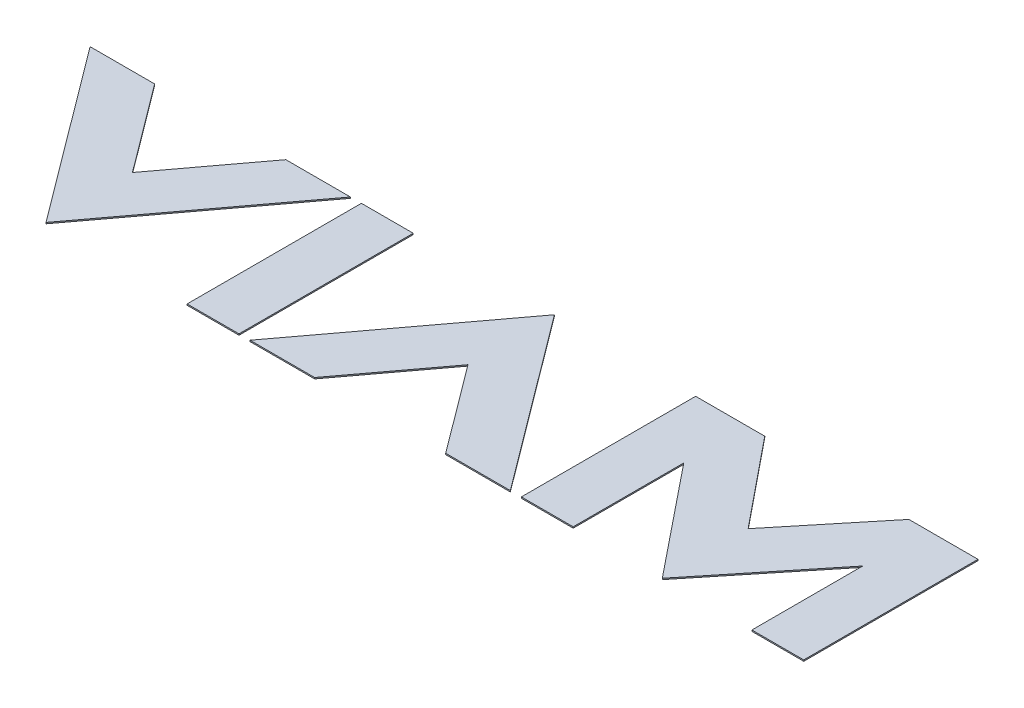
SolidWorks part; units mm, degrees
ref_plane "Front Plane" through (0, 0, 0) normal (0, 0, 1) x (1, 0, 0)
ref_plane "Top Plane" through (0, 0, 0) normal (0, 1, 0) x (1, 0, 0)
ref_plane "Right Plane" through (0, 0, 0) normal (1, 0, 0) x (0, 0, -1)
sketch "Sketch1" plane through (0, 0, 0) normal (0, 1, 0) x (1, 0, 0)
  line L0 (-15, 0) -> (15, 0) construction
  line L1 (-15, 10) -> (15, 10) construction
  line L2 (-15, -10) -> (15, -10) construction
  line L4 (37.5, -12.5) -> (-37.5, -12.5)
  line L5 (37.5, -12.5) -> (37.5, 12.5)
  line L6 (37.5, 12.5) -> (-37.5, 12.5)
  line L7 (-37.5, -12.5) -> (-37.5, 12.5)
  line L8 (37.5, -12.5) -> (-37.5, 12.5) construction
  line L9 (37.5, 12.5) -> (-37.5, -12.5) construction
  arc A0 (-15, 10) -> (-15, -10) centre (-15, 0) ccw construction
  arc A1 (15, -10) -> (15, 10) centre (15, 0) ccw construction
  point P2 (0, 0)
  point P8 (0, 0)
  dimension "D1" = 10
  dimension "D2" = 30
  dimension "D3" = 75
  dimension "D4" = 25
sketch "Sketch2" plane through (-16.7784, 0, 2.9159) normal (0, 1, 0) x (1, 0, 0)
  line L0 (2.563, 10.2) -> (6.7344, 10.2)
  line L1 (6.7344, 10.2) -> (6.7344, -3.8188)
  line L2 (6.7344, -3.8188) -> (2.563, -3.8188)
  line L3 (2.563, -3.8188) -> (2.563, 10.2)
  line L4 (46.612, 10.2) -> (40.7912, 3.0852)
  line L5 (40.7912, 3.0852) -> (35.0159, 10.2)
  line L6 (35.0159, 10.2) -> (29.4555, 10.2)
  line L7 (29.4555, 10.2) -> (29.4555, -3.8188)
  line L8 (29.4555, -3.8188) -> (33.6227, -3.8188)
  line L9 (33.6227, -3.8188) -> (33.6227, 5.0778)
  line L10 (33.6227, 5.0778) -> (40.7912, -3.8188)
  line L11 (40.7912, -3.8188) -> (48.0011, 5.0985)
  line L12 (48.0011, 5.0985) -> (48.0011, -3.8188)
  line L13 (48.0011, -3.8188) -> (52.1724, -3.8188)
  line L14 (52.1724, -3.8188) -> (52.1724, 10.2)
  line L15 (52.1724, 10.2) -> (46.612, 10.2)
  line L16 (-3.5183, 10.2) -> (-8.7934, 3.1348)
  line L17 (-8.7934, 3.1348) -> (-14.0685, 10.2)
  line L18 (-14.0685, 10.2) -> (-19.2651, 10.2)
  line L19 (-19.2651, 10.2) -> (-8.7934, -3.8188)
  line L20 (-8.7934, -3.8188) -> (1.6784, 10.2)
  line L21 (1.6784, 10.2) -> (-3.5183, 10.2)
  line L22 (18.095, 10.2) -> (7.6233, -3.8188)
  line L23 (7.6233, -3.8188) -> (12.8198, -3.8188)
  line L24 (12.8198, -3.8188) -> (18.095, 3.2423)
  line L25 (18.095, 3.2423) -> (23.3701, -3.8229)
  line L26 (23.3701, -3.8229) -> (28.5667, -3.8229)
  line L27 (28.5667, -3.8229) -> (18.095, 10.2)
extrude "Boss-Extrude3" add sketch "Sketch2" along normal blind 0.1
sketch "Sketch3" plane through (0, 0.1, 0) normal (0, 1, 0) x (1, 0, 0)
  line L0 (-61.5, 10.7) -> (61.5, 10.7)
  line L1 (-63.5, -12.7) -> (63.5, -12.7)
  line L2 (-63.5, -12.7) -> (-63.5, 12.7)
  line L3 (-63.5, 12.7) -> (63.5, 12.7)
  line L4 (63.5, -12.7) -> (63.5, 12.7)
  line L5 (-63.5, -12.7) -> (63.5, 12.7) construction
  line L6 (-63.5, 12.7) -> (63.5, -12.7) construction
  line L7 (61.5, -10.7) -> (61.5, 10.7)
  line L8 (-61.5, -10.7) -> (61.5, -10.7)
  line L9 (-61.5, -10.7) -> (-61.5, 10.7)
  point P0 (0, 0)
  dimension "D1" = 25.4
  dimension "D2" = 127
  dimension "D3" = 2
extrude "Boss-Extrude4" [suppressed] add sketch "Sketch3" along normal blind 0.1 separate body
